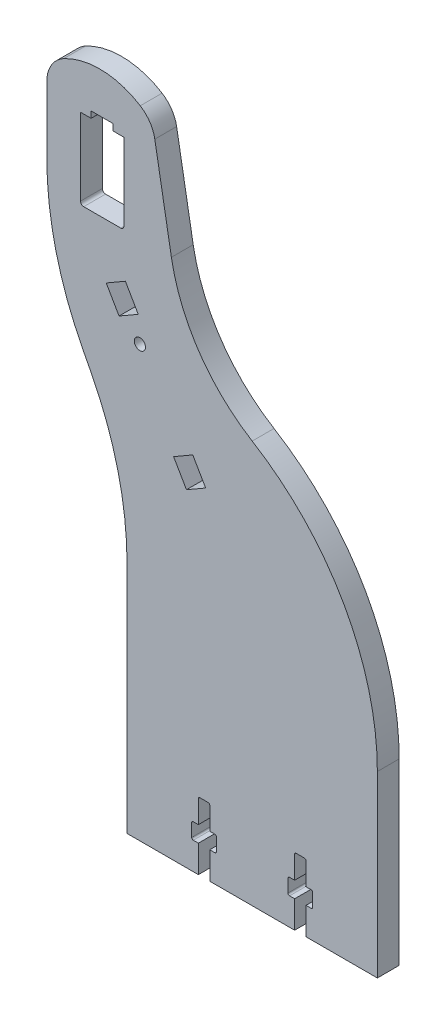
SolidWorks part; units mm, degrees
ref_plane "Front Plane" through (0, 0, 0) normal (0, 0, 1) x (1, 0, 0)
ref_plane "Top Plane" through (0, 0, 0) normal (0, 1, 0) x (1, 0, 0)
ref_plane "Right Plane" through (0, 0, 0) normal (1, 0, 0) x (0, 0, -1)
sketch "Sketch1" plane through (0, 0, 0) normal (0, 0, 1) x (1, 0, 0)
  line L0 (-103, 169.7984) -> (-103, 190.4365)
  line L1 (-89.2368, 118.8738) -> (-91.7632, 123.7432)
  line L2 (-64.1812, 162.4) -> (-69.3487, 191.7061)
  line L3 (0, 0) -> (0, 55.7267)
  line L4 (-78, 0) -> (-78, 72.8186)
  line L29 (0, 0) -> (-78, 0)
  arc A0 (-97.7305, 199.2469) -> (-103, 190.4365) centre (-93, 190.4365) ccw
  arc A1 (-103, 169.7984) -> (-91.7632, 123.7432) centre (-3, 169.7984) ccw
  arc A2 (-78, 72.8186) -> (-89.2368, 118.8738) centre (-178, 72.8186) ccw
  arc A3 (-64.1812, 162.4) -> (-39, 125.4) centre (-10.4994, 171.8655) ccw
  arc A4 (-69.3487, 191.7061) -> (-73.8816, 198.4401) centre (-79.1967, 189.9696) ccw
  arc A5 (-73.8816, 198.4401) -> (-97.7305, 199.2469) centre (-86.5, 178.3307) ccw
  arc A6 (0, 55.7267) -> (-39, 125.4) centre (-81.7355, 55.7267) ccw
  dimension "D2" = 81.7355
  dimension "D3" = 100
  dimension "D4" = 10
  dimension "D5" = 54.5099
  dimension "D6" = 23.7405
  dimension "D1" = 78
  dimension "D7" = 3
  dimension "D8" = 10.4994
  dimension "D9" = 64.1812
  dimension "D10" = 69.3487
  dimension "D11" = 73.8816
  dimension "D12" = 89.2368
  dimension "D13" = 55.7267
  dimension "D14" = 72.8186
extrude "Boss-Extrude1" add sketch "Sketch1" along normal blind 6.8
sketch "Sketch2" plane through (0, 0, 6.8) normal (0, 0, 1) x (1, 0, 0)
  line L0 (-78, 0) -> (0, 0) construction
  line L1 (-52.225, 0) -> (-55.775, 0)
  line L2 (-52.225, 0) -> (-52.225, 21)
  line L3 (-52.225, 21) -> (-55.775, 21)
  line L4 (-55.775, 0) -> (-55.775, 21)
  line L5 (-52.225, 0) -> (-55.775, 21) construction
  line L6 (-52.225, 21) -> (-55.775, 0) construction
  line L7 (-22.225, 0) -> (-25.775, 0)
  line L8 (-22.225, 0) -> (-22.225, 21)
  line L9 (-22.225, 21) -> (-25.775, 21)
  line L10 (-25.775, 0) -> (-25.775, 21)
  line L11 (-22.225, 0) -> (-25.775, 21) construction
  line L12 (-22.225, 21) -> (-25.775, 0) construction
  line L13 (0, 0) -> (0, 55.7267) construction
  line L15 (-57.86, 13.5) -> (-50.14, 13.5)
  line L16 (-57.86, 13.5) -> (-57.86, 8.5)
  line L17 (-57.86, 8.5) -> (-50.14, 8.5)
  line L18 (-50.14, 13.5) -> (-50.14, 8.5)
  line L19 (-57.86, 13.5) -> (-50.14, 8.5) construction
  line L20 (-57.86, 8.5) -> (-50.14, 13.5) construction
  line L21 (-27.86, 13.5) -> (-20.14, 13.5)
  line L22 (-27.86, 13.5) -> (-27.86, 8.5)
  line L23 (-27.86, 8.5) -> (-20.14, 8.5)
  line L24 (-20.14, 13.5) -> (-20.14, 8.5)
  line L25 (-27.86, 13.5) -> (-20.14, 8.5) construction
  line L26 (-27.86, 8.5) -> (-20.14, 13.5) construction
  point P0 (-54, 10.5)
  point P5 (-24, 10.5)
  point P14 (-54, 11)
  point P19 (-24, 11)
  line M18 (-78, 0) -> (0, 0)
  dimension "D1" = 3.55
  dimension "D2" = 21
  dimension "D3" = 30
  dimension "D4" = 24
  dimension "D5" = 8.5
  dimension "D6" = 7.72
  dimension "D7" = 5
extrude "Cut-Extrude1" cut sketch "Sketch2" against normal blind 6.8 contours L18 L15 L2 L17 | L4 L17 L2 L15 | L16 L17 L4 L15 | L17 L4 L2 M18 | L4 L15 L2 L3 | L22 L23 L10 L21 | L24 L21 L8 L23 | L10 L21 L8 L9 | L10 L23 L8 L21 | L23 L10 L8 M18
sketch "Sketch3" plane through (0, 0, 6.8) normal (0, 0, 1) x (1, 0, 0)
  line L0 (-89.2, 187.4) -> (-89.2, 189.4)
  line L1 (-79, 162.4) -> (-92.5, 162.4)
  line L2 (-79, 162.4) -> (-79, 187.4)
  line L3 (-79, 187.4) -> (-82.3, 187.4)
  line L4 (-92.5, 162.4) -> (-92.5, 187.4)
  line L5 (-79, 162.4) -> (-92.5, 187.4) construction
  line L6 (-79, 187.4) -> (-92.5, 162.4) construction
  line L7 (-89.2, 189.4) -> (-82.3, 189.4)
  line L8 (-82.3, 189.4) -> (-82.3, 187.4)
  line L9 (-89.2, 187.4) -> (-92.5, 187.4)
  line L10 (-78, 0) -> (-55.775, 0) construction
  line L11 (-103, 190.4365) -> (-103, 169.7984) construction
  point P0 (-85.75, 174.9)
  point P11 (-103, 180.1175)
  dimension "D1" = 13.5
  dimension "D2" = 25
  dimension "D3" = 6.9
  dimension "D4" = 3.3
  dimension "D5" = 162.4
  dimension "D6" = 10.5
  dimension "D7" = 2
extrude "Cut-Extrude2" cut sketch "Sketch3" against normal blind 6.8
sketch "Sketch4" plane through (0, 0, 6.8) normal (0, 0, 1) x (1, 0, 0)
  line L0 (-84.488, 145.3263) -> (-80.488, 138.3981)
  line L1 (-80.488, 138.3981) -> (-74.5124, 141.8481)
  line L2 (-74.5124, 141.8481) -> (-78.5124, 148.7763)
  line L3 (-78.5124, 148.7763) -> (-84.488, 145.3263)
  line L4 (-63.488, 108.9532) -> (-59.488, 102.025)
  line L5 (-59.488, 102.025) -> (-53.5124, 105.475)
  line L6 (-53.5124, 105.475) -> (-57.5124, 112.4032)
  line L7 (-57.5124, 112.4032) -> (-63.488, 108.9532)
  line L8 (-78, 0) -> (-55.775, 0) construction
  line L9 (-74.0002, 134.0609) -> (-81.5002, 147.0513) construction
  line L10 (-52.225, 0) -> (-25.775, 0) construction
  circle A0 centre (-74.0002, 134.0609) radius 1.75
  point P12 (-39, 0)
  dimension "D6" = 3.5
  dimension "D1" = 8
  dimension "D2" = 6.9
  dimension "D3" = 34
  dimension "D4" = 30
  dimension "D5" = 7
  dimension "D7" = 18.512
  dimension "D8" = 102.025
extrude "Cut-Extrude3" cut sketch "Sketch4" against normal blind 6.8
fillet "Fillet1" radius 1 2 edges at (-79, 162.4, 3.4) (-92.5, 162.4, 3.4)
fillet "Fillet2" radius 0.5 12 edges at (-50.14, 8.5, 3.4) (-57.86, 8.5, 3.4) (-57.86, 13.5, 3.4) (-50.14, 13.5, 3.4) (-55.775, 21, 3.4) (-52.225, 21, 3.4) (-20.14, 13.5, 3.4) (-20.14, 8.5, 3.4) (-27.86, 8.5, 3.4) (-27.86, 13.5, 3.4) (-25.775, 21, 3.4) (-22.225, 21, 3.4)
